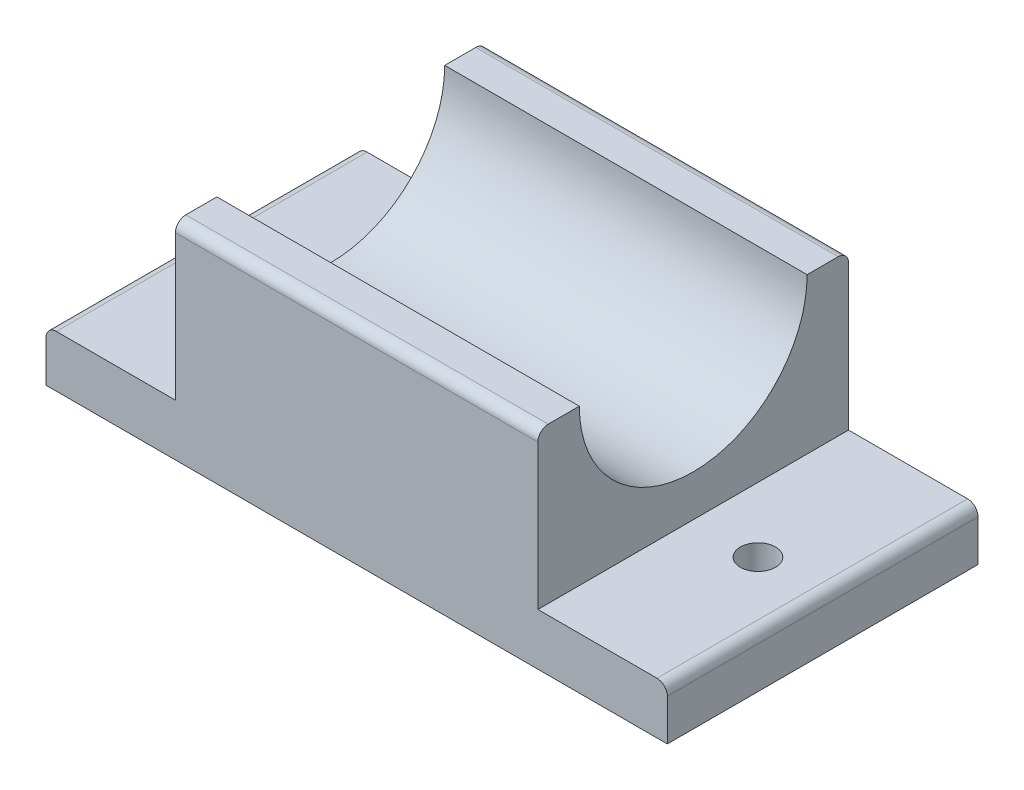
SolidWorks part; units mm, degrees
ref_plane "Front Plane" through (0, 0, 0) normal (0, 0, 1) x (1, 0, 0)
ref_plane "Top Plane" through (0, 0, 0) normal (0, 1, 0) x (1, 0, 0)
ref_plane "Right Plane" through (0, 0, 0) normal (1, 0, 0) x (0, 0, -1)
sketch "Sketch1" plane through (0, 0, 0) normal (0, 1, 0) x (1, 0, 0)
  line L1 (-17.6136, 19.0422) -> (42.3864, 19.0422)
  line L2 (-17.6136, 19.0422) -> (-17.6136, -10.9578)
  line L3 (-17.6136, -10.9578) -> (42.3864, -10.9578)
  line L4 (42.3864, 19.0422) -> (42.3864, -10.9578)
  dimension "D1" = 30
  dimension "D2" = 60
extrude "Boss-Extrude1" add sketch "Sketch1" along normal blind 5
sketch "Sketch2" plane through (0, 5, 0) normal (0, 1, 0) x (1, 0, 0)
  line L0 (42.3864, 19.0422) -> (-17.6136, 19.0422) construction
  line L1 (-5.1136, 19.0422) -> (29.8864, 19.0422)
  line L2 (-5.1136, 19.0422) -> (-5.1136, -10.9578)
  line L3 (-5.1136, -10.9578) -> (29.8864, -10.9578)
  line L4 (29.8864, 19.0422) -> (29.8864, -10.9578)
  line L5 (-17.6136, -10.9578) -> (42.3864, -10.9578) construction
  point P8 (12.3864, -10.9578)
  point P9 (12.3864, -10.9578)
  dimension "D1" = 35
extrude "Boss-Extrude2" add sketch "Sketch2" along normal blind 15
sketch "Sketch4" plane through (29.8864, 0, 0) normal (1, 0, 0) x (0, 0, -1)
  line L0 (-10.9578, 20) -> (19.0422, 20) construction
  circle A0 centre (4.0422, 20) radius 11
  dimension "D1" = 22
extrude "Cut-Extrude1" cut sketch "Sketch4" against normal through all
hole_wizard "M3 Clearance Hole1" positions "Sketch7" profile "Sketch8" hole size "M3" standard "ANSI Metric" end condition through all
sketch "Sketch7" plane through (0, 5, 0) normal (0, 1, 0) x (1, 0, 0)
  line L0 (-17.6136, 19.0422) -> (-17.6136, -10.9578) construction
  line L1 (-17.6136, -10.9578) -> (-5.1136, -10.9578) construction
  line L2 (29.8864, -10.9578) -> (42.3864, -10.9578) construction
  point P2 (36.1364, 4.0422)
  point P10 (-11.3636, 4.0422)
  point P15 (-17.6136, 4.0422)
  point P18 (-11.3636, -10.9578)
  point P21 (36.1364, -10.9578)
sketch "Sketch8" plane through (36.1364, 5, -4.0422) normal (1, 0, 0) x (0, 0, 1)
  line L0 (0, 0) -> (0, 5)
  line L1 (0, 5) -> (1.7, 5)
  line L2 (1.7, 5) -> (1.7, 0)
  line L5 (1.7, 0) -> (0, 0)
  line L11 (0, -6.35) -> (0, 107.95) construction
  dimension "Thru Hole Dia." = 3.4
  dimension "Thru Hole Depth" = 5
fillet "Fillet1" radius 1 1 edges at (12.3864, 20, 10.9578)
fillet "Fillet2" radius 1 1 edges at (12.3864, 20, -19.0422)
ref_plane "Plane1" through (-17.6136, 5, -19.0422) normal (0, 0, 1) x (1, 0, 0)
fillet "Fillet3" radius 1 1 edges at (42.3864, 5, -4.0422)
fillet "Fillet4" radius 1 1 edges at (-17.6136, 5, -4.0422)
